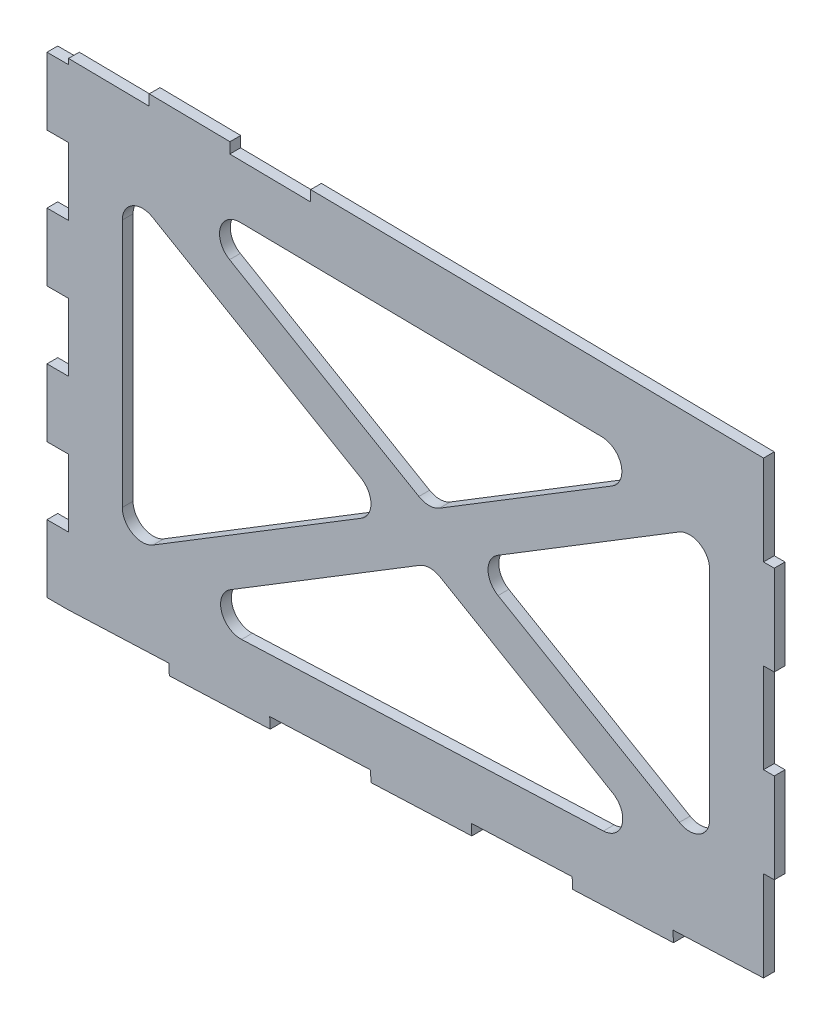
SolidWorks part; units mm, degrees
material "A-Glass Fiber"
ref_plane "Front Plane" through (0, 0, 0) normal (0, 0, 1) x (1, 0, 0)
ref_plane "Top Plane" through (0, 0, 0) normal (0, 1, 0) x (1, 0, 0)
ref_plane "Right Plane" through (0, 0, 0) normal (1, 0, 0) x (0, 0, -1)
sketch "Sketch1" plane through (0, 0, 0) normal (0, 0, 1) x (1, 0, 0)
  line L0 (20.32, 10.1649) -> (781.2461, 41.6972)
  line L1 (781.2461, 41.6972) -> (781.6666, 31.5497)
  line L2 (686.4983, 27.606) -> (781.6666, 31.5497)
  line L3 (20.32, 10.1649) -> (20.32, 328.5902)
  line L4 (20.32, 328.5902) -> (20.269, 455.9603)
  line L5 (20.32, 328.5902) -> (0, 328.5902)
  line L6 (20.32, 328.5902) -> (20.32, 10.1649)
  line L9 (781.2461, 41.6972) -> (778.0911, 117.8318)
  line L11 (20.32, 0) -> (115.4883, 3.9437)
  line L12 (0, 328.5902) -> (20.32, 328.5902)
  line L13 (0, 328.5902) -> (0, 264.9051)
  line L14 (0, 264.9051) -> (20.32, 264.9051)
  line L15 (20.32, 328.5902) -> (20.32, 264.9051)
  line L16 (20.32, 264.9051) -> (0, 264.9051)
  line L17 (20.32, 264.9051) -> (20.32, 201.2201)
  line L18 (20.32, 201.2201) -> (0, 201.2201)
  line L19 (0, 264.9051) -> (0, 201.2201)
  line L20 (0, 201.2201) -> (20.32, 201.2201)
  line L21 (0, 201.2201) -> (0, 137.535)
  line L22 (0, 137.535) -> (20.32, 137.535)
  line L23 (20.32, 201.2201) -> (20.32, 137.535)
  line L24 (20.32, 137.535) -> (0, 137.535)
  line L25 (20.32, 137.535) -> (20.32, 73.85)
  line L26 (20.32, 73.85) -> (0, 73.85)
  line L27 (0, 137.535) -> (0, 73.85)
  line L28 (0, 73.85) -> (20.32, 73.85)
  line L29 (0, 73.85) -> (0, 10.1649)
  line L31 (20.32, 73.85) -> (20.32, 0)
  line L33 (115.4883, 3.9437) -> (115.0678, 14.0912)
  line L34 (20.32, 10.1649) -> (115.0678, 14.0912)
  line L35 (115.4883, 3.9437) -> (115.0678, 14.0912)
  line L36 (115.4883, 3.9437) -> (210.6566, 7.8874)
  line L37 (115.0678, 14.0912) -> (210.2361, 18.0349)
  line L38 (210.6566, 7.8874) -> (210.2361, 18.0349)
  line L39 (210.2361, 18.0349) -> (210.6566, 7.8874)
  line L40 (210.2361, 18.0349) -> (305.4045, 21.9786)
  line L41 (210.6566, 7.8874) -> (305.825, 11.8311)
  line L42 (305.4045, 21.9786) -> (305.825, 11.8311)
  line L43 (305.4045, 21.9786) -> (305.825, 11.8311)
  line L44 (305.4045, 21.9786) -> (400.5728, 25.9223)
  line L45 (305.825, 11.8311) -> (400.9933, 15.7748)
  line L46 (400.5728, 25.9223) -> (400.9933, 15.7748)
  line L47 (400.9933, 15.7748) -> (400.5728, 25.9223)
  line L48 (400.9933, 15.7748) -> (496.1616, 19.7186)
  line L49 (400.5728, 25.9223) -> (495.7411, 29.866)
  line L50 (496.1616, 19.7186) -> (495.7411, 29.866)
  line L51 (495.7411, 29.866) -> (496.1616, 19.7186)
  line L52 (495.7411, 29.866) -> (590.9094, 33.8097)
  line L53 (496.1616, 19.7186) -> (591.3299, 23.6623)
  line L54 (590.9094, 33.8097) -> (591.3299, 23.6623)
  line L55 (590.9094, 33.8097) -> (591.3299, 23.6623)
  line L56 (590.9094, 33.8097) -> (686.0778, 37.7535)
  line L57 (591.3299, 23.6623) -> (686.4983, 27.606)
  line L58 (686.0778, 37.7535) -> (686.4983, 27.606)
  line L59 (20.32, 10.1649) -> (0, 10.1649)
  line L60 (20.32, 10.1649) -> (20.32, 0)
  line L61 (20.32, 0) -> (0, 0) construction
  line L62 (0, 0) -> (0, 10.1649) construction
  line L63 (781.2461, 41.6972) -> (781.2461, 471.9516)
  line L64 (20.32, 328.5902) -> (0, 328.5902)
  line L65 (20.32, 328.5902) -> (20.32, 392.2753)
  line L66 (0, 328.5902) -> (0, 392.2753)
  line L67 (20.32, 392.2753) -> (0, 392.2753)
  line L68 (20.32, 392.2753) -> (0, 392.2753)
  line L69 (20.32, 392.2753) -> (20.32, 455.9603)
  line L70 (0, 392.2753) -> (0, 455.9603)
  line L71 (20.32, 455.9603) -> (0, 455.9603)
  line L72 (20.32, 455.9603) -> (0, 455.9603)
  line L73 (20.32, 455.9603) -> (20.32, 519.6454)
  line L74 (0, 455.9603) -> (0, 519.6454)
  line L75 (20.32, 519.6454) -> (0, 519.6454)
  line L76 (20.32, 328.5902) -> (20.32, 519.6454)
  arc A0 (1445.699, 402.1929) -> (-664.1875, 533.4087) centre (-664.1875, -16495.1746) ccw construction
  arc A1 (25.4125, 0.0087) -> (1875.8125, 190.5087) centre (25.4125, 9082.0833) ccw construction
  arc A2 (781.2461, 471.9516) -> (20.32, 519.6454) centre (-664.1875, -16495.1746) ccw
  dimension "D1" = 762
  dimension "D4" = 76.2
  dimension "D5" = 20.32
  dimension "D7" = 10.1562
extrude "Boss-Extrude1" add sketch "Sketch1" along normal blind 10.16
sketch "Sketch2" plane through (0, 0, 10.16) normal (0, 0, 1) x (1, 0, 0)
  line L0 (20.32, 471.239) -> (781.2461, 460.9484)
  line L1 (20.32, 455.9603) -> (20.32, 519.6454) construction
  line L2 (781.2461, 41.6972) -> (781.2461, 471.9516) construction
  line L3 (20.32, 471.239) -> (20.32, 535.0179)
  line L4 (20.32, 535.0179) -> (781.2461, 535.0179)
  line L5 (781.2461, 535.0179) -> (781.2461, 460.9484)
  point P6 (116.1565, 0)
  dimension "D1" = 469.9
extrude "Cut-Extrude1" cut sketch "Sketch2" against normal through all
sketch "Sketch3" plane through (0, 0, 0) normal (0, 0, -1) x (-1, 0, 0)
  line L2 (-20.32, 471.239) -> (-781.2461, 460.9484) construction
  line L3 (-96.52, 470.2085) -> (-20.32, 471.239)
sketch "Sketch4" plane through (0, 0, 0) normal (0, 0, -1) x (-1, 0, 0)
  line L1 (-686.4983, 27.606) -> (-816.0458, 27.606)
  line L2 (-686.4983, 27.606) -> (-686.4983, 471.6431)
  line L3 (-686.4983, 471.6431) -> (-816.0458, 471.6431)
  line L4 (-816.0458, 27.606) -> (-816.0458, 471.6431)
extrude "Cut-Extrude3" cut sketch "Sketch4" against normal through all
sketch "Sketch5" plane through (0, 0, 0) normal (0, 0, -1) x (-1, 0, 0)
  line L0 (-686.4983, 27.606) -> (-686.4983, 462.2297) construction
  line L1 (-686.4983, 37.7535) -> (-676.3383, 37.7535)
  line L2 (-686.4983, 37.7535) -> (-686.4983, 122.6762)
  line L3 (-686.4983, 122.6762) -> (-676.3383, 122.6762)
  line L4 (-676.3383, 37.7535) -> (-676.3383, 122.6762)
  line L5 (-20.32, 471.239) -> (-686.4983, 462.2297) construction
  line L6 (-686.4983, 122.6762) -> (-676.3383, 122.6762)
  line L7 (-686.4983, 122.6762) -> (-686.4983, 207.5989)
  line L8 (-686.4983, 207.5989) -> (-676.3383, 207.5989)
  line L9 (-676.3383, 122.6762) -> (-676.3383, 207.5989)
  line L10 (-686.4983, 207.5989) -> (-676.3383, 207.5989)
  line L11 (-686.4983, 207.5989) -> (-686.4983, 292.5217)
  line L12 (-686.4983, 292.5217) -> (-676.3383, 292.5217)
  line L13 (-676.3383, 207.5989) -> (-676.3383, 292.5217)
  line L14 (-686.4983, 292.5217) -> (-676.3383, 292.5217)
  line L15 (-686.4983, 292.5217) -> (-686.4983, 377.4444)
  line L16 (-686.4983, 377.4444) -> (-676.3383, 377.4444)
  line L17 (-676.3383, 292.5217) -> (-676.3383, 377.4444)
  line L18 (-686.4983, 377.4444) -> (-676.3383, 377.4444)
  line L19 (-686.4983, 377.4444) -> (-686.4983, 462.3671)
  line L20 (-686.4983, 462.3671) -> (-676.3383, 462.3671)
  line L21 (-676.3383, 377.4444) -> (-676.3383, 462.3671)
  line L23 (-686.4983, 37.7535) -> (-676.3383, 37.7535)
  line L24 (-686.4983, 37.7535) -> (-686.4983, 26.1578)
  line L25 (-686.4983, 26.1578) -> (-676.3383, 26.1578)
  line L26 (-676.3383, 37.7535) -> (-676.3383, 26.1578)
  line M9 (-20.32, 471.239) -> (-686.4983, 462.2297)
  line M10 (-686.4983, 462.2297) -> (-686.4983, 27.606)
  line M11 (-686.4983, 27.606) -> (-686.0778, 37.7535)
  line M12 (-686.0778, 37.7535) -> (-590.9094, 33.8097)
  dimension "D1" = 10.16
extrude "Cut-Extrude5" cut sketch "Sketch5" against normal through all contours L1 L4 L3 M10 | L8 L13 L12 M10 | L16 L21 M9 M10 | L26 L24 L25 M12 M11 | L1 M10 M11 | L26 L1 M12
sketch "Sketch9" plane through (0, 0, 0) normal (0, 0, -1) x (-1, 0, 0)
  line L9 (-20.32, 455.9603) -> (-20.32, 471.239) construction
  line L11 (-20.32, 455.9603) -> (-20.32, 471.239)
  line L13 (-20.32, 471.239) -> (-676.3383, 462.3671) construction
  line L14 (-20.32, 471.239) -> (-676.3383, 462.3671)
  line L16 (-20.32, 471.239) -> (-96.513, 470.2086)
  line L17 (-20.32, 471.239) -> (-20.32, 461.079)
  line L18 (-20.32, 461.079) -> (-96.3757, 460.0505)
  line L19 (-96.513, 470.2086) -> (-96.3757, 460.0505)
  line L20 (-172.7061, 469.1782) -> (-172.5756, 459.019)
  line L21 (-172.5756, 459.019) -> (-248.7687, 457.9886)
  line L22 (-248.7687, 457.9886) -> (-248.9061, 468.1477)
  line L23 (-248.9061, 468.1477) -> (-172.7061, 469.1782)
  point P3 (-20.32, 471.239)
  dimension "D1" = 10.16
  dimension "D2" = 76.2
  dimension "D3" = 10.16
  dimension "D4" = 76.2
  dimension "D5" = 10.16
  dimension "D6" = 76.2
  dimension "D7" = 656.0183
  dimension "D8" = 76.2
extrude "Cut-Extrude6" cut sketch "Sketch9" against normal through all
sketch "Sketch10" plane through (0, 0, 10.16) normal (0, 0, 1) x (1, 0, 0)
  line L0 (676.3383, 452.21) -> (20.32, 461.0819)
  line L1 (676.3383, 377.4444) -> (676.3383, 462.3671) construction
  line L4 (20.32, 461.0819) -> (20.32, 10.1649)
  line L5 (20.32, 10.1649) -> (676.3383, 37.3499)
  line L6 (676.3383, 37.3499) -> (676.3383, 452.21)
  line L7 (71.12, 409.5903) -> (71.12, 63.1136)
  line L8 (71.12, 63.1136) -> (625.5383, 86.0883)
  line L9 (625.5383, 86.0883) -> (625.5383, 402.0924)
  line L10 (625.5383, 402.0924) -> (71.12, 409.5903)
  line L11 (71.12, 409.5903) -> (625.5383, 86.0883)
  line L12 (625.5383, 402.0924) -> (71.12, 63.1136)
  line L13 (589.809, 402.5756) -> (71.12, 85.4422)
  line L14 (71.12, 387.5345) -> (590.2454, 84.6258)
  line L15 (625.5383, 379.7638) -> (110.2947, 64.737)
  line L16 (109.8162, 409.067) -> (625.5383, 108.1442)
  line L17 (615.6011, 418.3452) -> (61.1828, 79.3664) construction
  line L18 (61.5192, 393.1365) -> (615.9375, 69.6345) construction
  line L19 (80.7208, 426.0441) -> (635.139, 102.5421) construction
  line L20 (635.4755, 385.8396) -> (81.0572, 46.8608) construction
  dimension "D1" = 50.8
  dimension "D2" = 19.05
  dimension "D3" = 19.05
extrude "Cut-Extrude7" cut sketch "Sketch10" against normal through all contours L14 L7 L13 | L10 L16 L13 | L15 L16 L9 | L14 L15 L8
fillet "Fillet1" radius 19.05 12 edges at (625.5383, 379.7638, 5.08) (398.2246, 240.7812, 5.08) (625.5383, 108.1442, 5.08) (590.2454, 84.6258, 5.08) (361.3084, 218.2101, 5.08) (110.2947, 64.737, 5.08) (71.12, 85.4422, 5.08) (323.9356, 240.0171, 5.08) (71.12, 387.5345, 5.08) (109.8162, 409.067, 5.08) (589.809, 402.5756, 5.08) (360.8519, 262.5882, 5.08)
